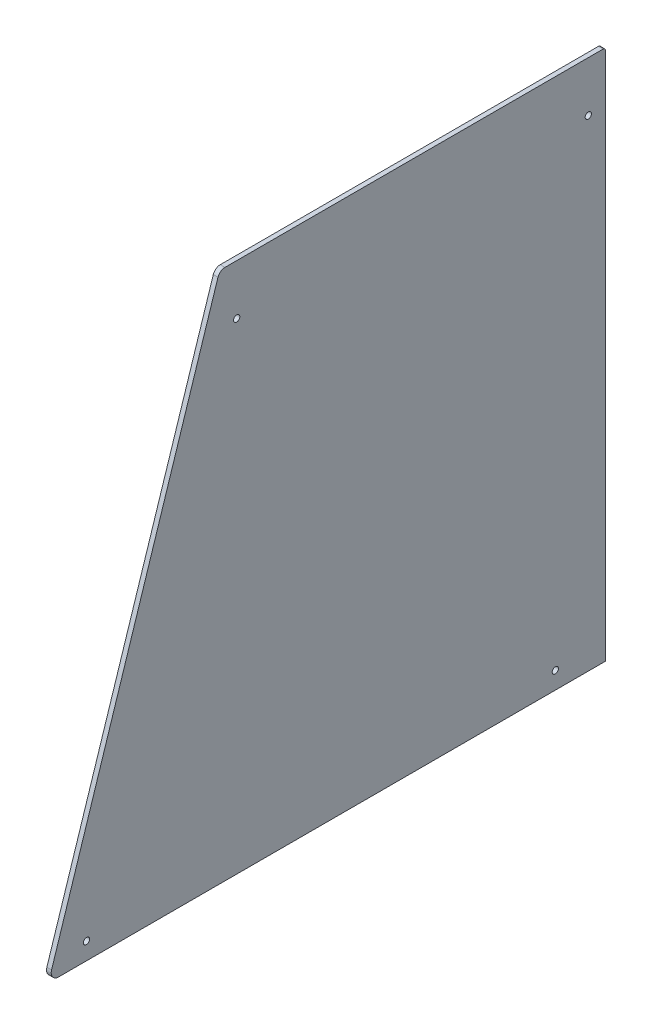
SolidWorks part; units mm, degrees
ref_plane "Front Plane" through (0, 0, 0) normal (0, 0, 1) x (1, 0, 0)
ref_plane "Top Plane" through (0, 0, 0) normal (0, 1, 0) x (1, 0, 0)
ref_plane "Right Plane" through (0, 0, 0) normal (1, 0, 0) x (0, 0, -1)
sketch "Sketch1" plane through (110.5, 0, 0) normal (1, 0, 0) x (0, 0, -1)
  line L0 (122.5, 328.5) -> (122.5, -10)
  line L1 (122.5, 310) -> (122.5, 328.5) construction
  line L2 (122.5, -10) -> (-227.5, -10)
  line L3 (-231.9672, -3.8678) -> (-125.4686, 326.7458)
  line L4 (-121.0014, 330) -> (121, 330)
  arc A0 (-227.5, -10) -> (-231.9672, -3.8678) centre (-227.5, -5.3068) cw
  arc A1 (-125.4686, 326.7458) -> (-121.0014, 330) centre (-121.0014, 325.3068) cw
  arc A2 (-121.0014, 330) -> (-125.4686, 326.7458) centre (-121.0014, 325.3068) ccw construction
  arc A3 (121, 330) -> (122.5, 328.5) centre (121, 328.5) cw
extrude "Boss-Extrude1" add sketch "Sketch1" against normal blind 3
sketch "Sketch2" plane through (110.5, 0, 0) normal (1, 0, 0) x (0, 0, -1)
  circle A0 centre (111.5014, 297.911) radius 2
  circle A1 centre (90.411, 0.9986) radius 2
  circle A2 centre (-209.589, 0.9986) radius 2
  circle A3 centre (-113.4986, 297.911) radius 2
  dimension "D1" = 4
  dimension "D2" = 300
extrude "Cut-Extrude2" cut sketch "Sketch2" against normal up to next
